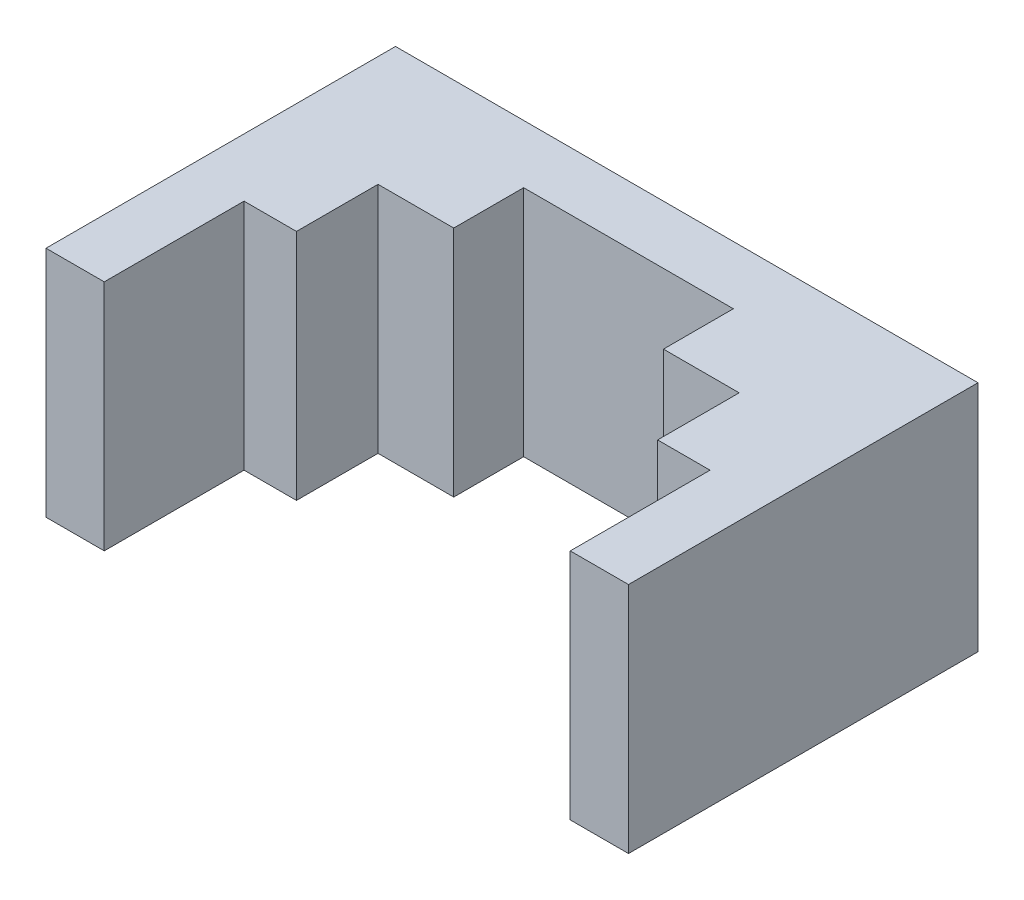
SolidWorks part; units mm, degrees
ref_plane "Front" through (0, 0, 0) normal (0, 0, 1) x (1, 0, 0)
ref_plane "Top" through (0, 0, 0) normal (0, 1, 0) x (1, 0, 0)
ref_plane "Right" through (0, 0, 0) normal (1, 0, 0) x (0, 0, -1)
other "Configuration Table"
sketch "Sketch1" plane through (0, 0, 0) normal (0, 0, 1) x (1, 0, 0)
  line L1 (-12.5, 5) -> (12.5, 5)
  line L2 (-12.5, 5) -> (-12.5, -5)
  line L3 (-12.5, -5) -> (12.5, -5)
  line L4 (12.5, 5) -> (12.5, -5)
  line L5 (-12.5, 5) -> (12.5, -5) construction
  line L6 (-12.5, -5) -> (12.5, 5) construction
  point P0 (0, 0)
extrude "Boss-Extrude1" add sketch "Sketch1" along normal blind 15
sketch "Sketch2" plane through (0, 0, 15) normal (0, 0, 1) x (1, 0, 0)
  line L0 (-12.5, -5) -> (12.5, -5) construction
  line L1 (-10, 5) -> (10, 5)
  line L2 (-10, 5) -> (-10, -5)
  line L3 (-10, -5) -> (10, -5)
  line L4 (10, 5) -> (10, -5)
  line L5 (-10, 5) -> (10, -5) construction
  line L6 (-10, -5) -> (10, 5) construction
  point P0 (0, 0)
extrude "Cut-Extrude1" cut sketch "Sketch2" against normal blind 6
sketch "Sketch3" plane through (0, 0, 9) normal (0, 0, 1) x (1, 0, 0)
  line L0 (-10, -5) -> (10, -5) construction
  line L1 (-4.5, 5) -> (4.5, 5)
  line L2 (-4.5, 5) -> (-4.5, -5)
  line L3 (-4.5, -5) -> (4.5, -5)
  line L4 (4.5, 5) -> (4.5, -5)
  line L5 (-4.5, 5) -> (4.5, -5) construction
  line L6 (-4.5, -5) -> (4.5, 5) construction
  point P0 (0, 0)
extrude "Cut-Extrude2" cut sketch "Sketch3" against normal blind 6.5
sketch "Sketch4" plane through (0, 0, 9) normal (0, 0, 1) x (1, 0, 0)
  line L0 (4.5, -5) -> (10, -5) construction
  line L1 (-7.75, 5) -> (7.75, 5)
  line L2 (-7.75, 5) -> (-7.75, -5)
  line L3 (-7.75, -5) -> (7.75, -5)
  line L4 (7.75, 5) -> (7.75, -5)
  line L5 (-7.75, 5) -> (7.75, -5) construction
  line L6 (-7.75, -5) -> (7.75, 5) construction
  point P0 (0, 0)
extrude "Cut-Extrude3" cut sketch "Sketch4" against normal blind 3.5
